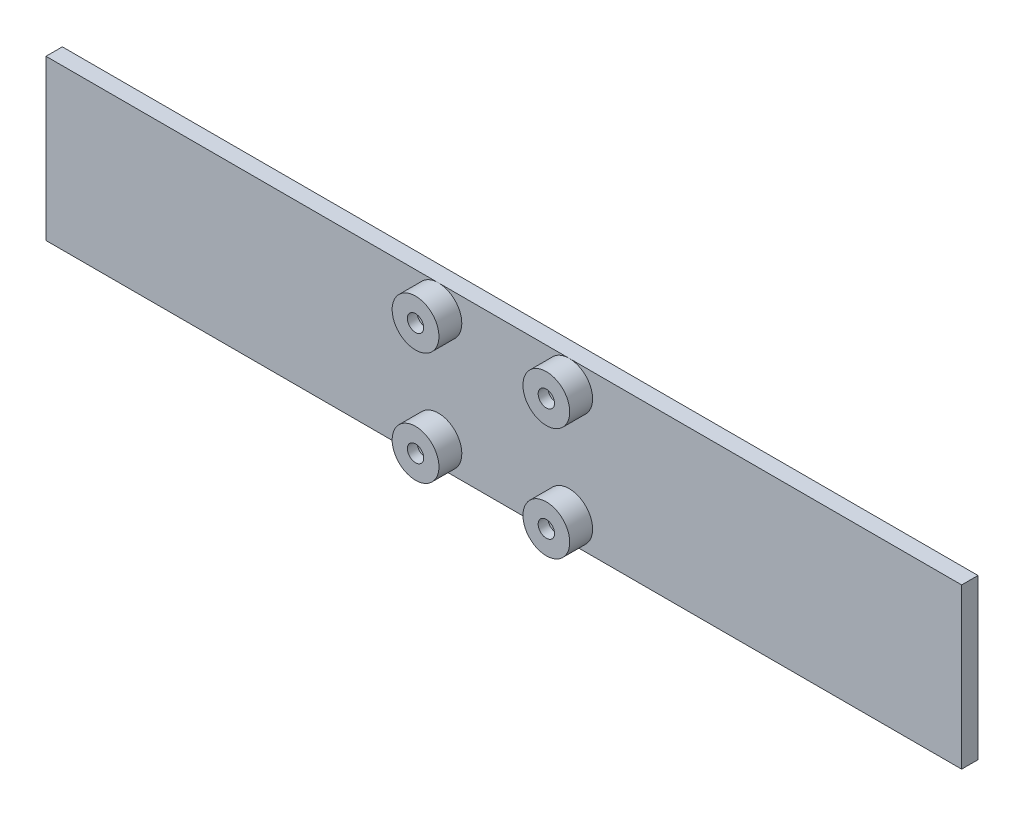
SolidWorks part; units mm, degrees
ref_plane "Front Plane" through (0, 0, 0) normal (0, 0, 1) x (1, 0, 0)
ref_plane "Top Plane" through (0, 0, 0) normal (0, 1, 0) x (1, 0, 0)
ref_plane "Right Plane" through (0, 0, 0) normal (1, 0, 0) x (0, 0, -1)
sketch "Sketch1" plane through (0, 0, 0) normal (0, 0, 1) x (1, 0, 0)
  line L1 (-121.5852, 35.7673) -> (158.4148, 35.7673)
  line L2 (-121.5852, 35.7673) -> (-121.5852, -13.0327)
  line L3 (-121.5852, -13.0327) -> (158.4148, -13.0327)
  line L4 (158.4148, 35.7673) -> (158.4148, -13.0327)
  dimension "D1" = 280
  dimension "D2" = 48.8
extrude "Boss-Extrude1" add sketch "Sketch1" along normal blind 4
sketch "Sketch2" plane through (0, 0, 4) normal (0, 0, 1) x (1, 0, 0)
  line L0 (18.4148, 35.7673) -> (18.4148, -13.0327) construction
  line L1 (158.4148, 35.7673) -> (-121.5852, 35.7673) construction
  line L2 (-121.5852, -13.0327) -> (158.4148, -13.0327) construction
  line L4 (-1.5852, 28.6173) -> (38.4148, 28.6173)
  line L5 (-1.5852, 28.6173) -> (-1.5852, -5.8827)
  line L6 (-1.5852, -5.8827) -> (38.4148, -5.8827)
  line L7 (38.4148, 28.6173) -> (38.4148, -5.8827)
  circle A0 centre (-1.5852, 28.6173) radius 5.25
  circle A1 centre (38.4148, 28.6173) radius 5.25
  circle A2 centre (38.4148, -5.8827) radius 5.25
  circle A3 centre (-1.5852, -5.8827) radius 5.25
  dimension "D1" = 10.5
  dimension "D2" = 7.15
  dimension "D3" = 40
  dimension "D4" = 20
  dimension "D5" = 7.15
extrude "Cut-Extrude1" cut sketch "Sketch2" against normal through all contours L4 A0 L5 | L5 A0 L4 | L5 A3 L6 | L6 A3 L5 | L6 A2 L7 | L7 A2 L6 | L7 A1 L4 | L4 A1 L7
sketch "Sketch3" plane through (0, 0, 4) normal (0, 0, 1) x (1, 0, 0)
  circle A0 centre (-1.5852, 28.6173) radius 7.15
  circle A1 centre (38.4148, 28.6173) radius 7.15
  circle A2 centre (-1.5852, -5.8827) radius 7.15
  circle A3 centre (38.4148, -5.8827) radius 7.15
  circle A4 centre (-1.5852, -5.8827) radius 5.25
  circle A5 centre (-1.5852, 28.6173) radius 5.25
  circle A6 centre (38.4148, 28.6173) radius 5.25
  circle A7 centre (38.4148, -5.8827) radius 5.25
  circle A8 centre (-1.5852, 28.6173) radius 5.25 construction
extrude "Boss-Extrude2" add sketch "Sketch3" along normal blind 8
sketch "Sketch4" plane through (0, 0, 12) normal (0, 0, 1) x (1, 0, 0)
  circle A0 centre (-1.5852, 28.6173) radius 7.15
  circle A1 centre (38.4148, 28.6173) radius 7.15
  circle A2 centre (-1.5852, -5.8827) radius 7.15
  circle A3 centre (38.4148, -5.8827) radius 7.15
  circle A4 centre (-1.5852, 28.6173) radius 2.5
  circle A5 centre (38.4148, 28.6173) radius 2.5
  circle A6 centre (38.4148, -5.8827) radius 2.5
  circle A7 centre (-1.5852, -5.8827) radius 2.5
  dimension "D1" = 5
extrude "Boss-Extrude3" add sketch "Sketch4" against normal blind 3
sketch "Sketch5" plane through (0, 0, 4) normal (0, 0, 1) x (1, 0, 0)
  line L1 (-121.5852, 35.7673) -> (158.4148, 35.7673)
  line L2 (-121.5852, 35.7673) -> (-121.5852, -13.0327)
  line L3 (-121.5852, -13.0327) -> (158.4148, -13.0327)
  line L4 (158.4148, 35.7673) -> (158.4148, -13.0327)
extrude "Boss-Extrude6" add sketch "Sketch5" along normal blind 1
sketch "Sketch6" plane through (0, 0, 4) normal (0, 0, -1) x (-1, 0, 0)
  circle A0 centre (-38.4148, 28.6173) radius 5.25
  circle A1 centre (1.5852, 28.6173) radius 5.25
  circle A2 centre (1.5852, -5.8827) radius 5.25
  circle A3 centre (-38.4148, -5.8827) radius 5.25
extrude "Cut-Extrude2" cut sketch "Sketch6" against normal blind 1 contours A1 | A2 | A0 | A3
